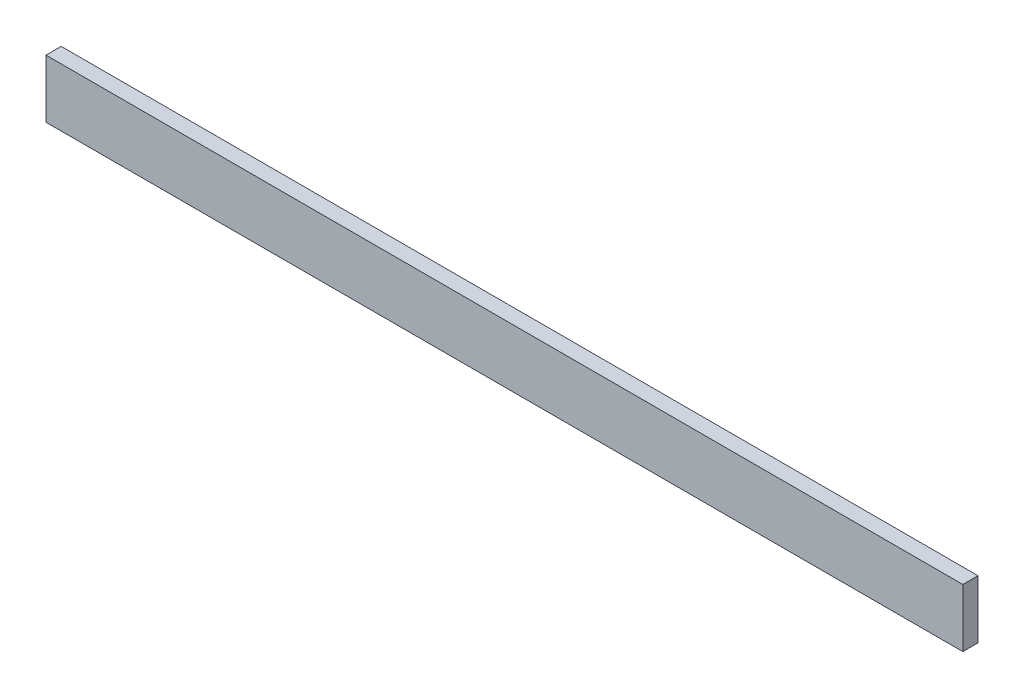
SolidWorks part; units mm, degrees
ref_plane "Front Plane" through (0, 0, 0) normal (0, 0, 1) x (1, 0, 0)
ref_plane "Top Plane" through (0, 0, 0) normal (0, 1, 0) x (1, 0, 0)
ref_plane "Right Plane" through (0, 0, 0) normal (1, 0, 0) x (0, 0, -1)
sketch "Sketch1" plane through (0, 0, 0) normal (0, 0, 1) x (1, 0, 0)
  line L0 (0, 0) -> (603.6417, 0)
  line L1 (603.6417, 0) -> (603.6417, 38.2926)
  line L2 (603.6417, 38.2926) -> (0, 38.2926)
  line L3 (0, 38.2926) -> (0, 0)
extrude "Boss-Extrude1" add sketch "Sketch1" along normal blind 10
